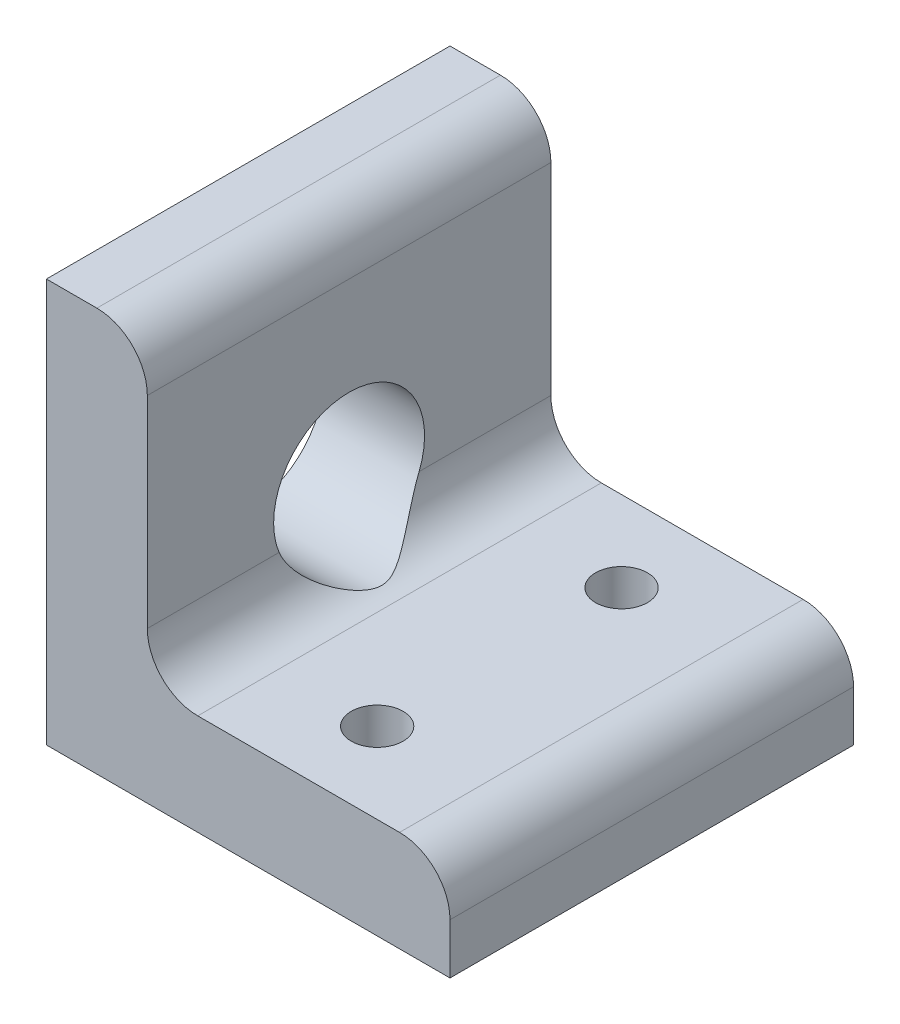
SolidWorks part; units mm, degrees
ref_plane "Front Plane" through (0, 0, 0) normal (0, 0, 1) x (1, 0, 0)
ref_plane "Top Plane" through (0, 0, 0) normal (0, 1, 0) x (1, 0, 0)
ref_plane "Right Plane" through (0, 0, 0) normal (1, 0, 0) x (0, 0, -1)
sketch "Sketch1" plane through (0, 0, 0) normal (0, 0, 1) x (1, 0, 0)
  line L1 (0, 0) -> (25.4, 0)
  line L2 (0, 0) -> (0, 25.4)
  line L3 (0, 25.4) -> (25.4, 25.4)
  line L4 (25.4, 0) -> (25.4, 25.4)
  line L5 (25.4, 25.4) -> (6.35, 25.4)
  line L6 (25.4, 25.4) -> (25.4, 6.35)
  line L7 (25.4, 6.35) -> (6.35, 6.35)
  line L8 (6.35, 25.4) -> (6.35, 6.35)
  dimension "D1" = 25.4
  dimension "D2" = 25.4
  dimension "D3" = 19.05
  dimension "D4" = 19.05
extrude "Boss-Extrude1" add sketch "Sketch1" along normal blind 25.4 contours L8 L3 L2 L1 L4 L7
hole_wizard "#4 Clearance Hole1" positions "Sketch5" profile "Sketch4" hole size "#4" standard "ANSI Inch" end condition through all
sketch "Sketch5" plane through (0, 6.35, 0) normal (0, 1, 0) x (1, 0, 0)
  point P0 (15.7352, -20.32)
  point P2 (15.875, -5.08)
  dimension "D1" = 15.875
  dimension "D2" = 15.7352
  dimension "D3" = 5.08
  dimension "D4" = 20.32
sketch "Sketch4" plane through (15.7352, 6.35, 20.32) normal (1, 0, 0) x (0, 0, 1)
  line L0 (0, 0) -> (0, 6.35)
  line L1 (0, 6.35) -> (1.6319, 6.35)
  line L2 (1.6319, 6.35) -> (1.6319, 0)
  line L5 (1.6319, 0) -> (0, 0)
  line L11 (0, -6.35) -> (0, 107.95) construction
  dimension "Thru Hole Dia." = 3.2639
  dimension "Thru Hole Depth" = 6.35
fillet "Fillet1" radius 3.175 3 edges at (25.4, 6.35, 12.7) (6.35, 6.35, 12.7) (6.35, 25.4, 12.7)
hole_wizard "3/8 (0.374) Diameter Hole1" positions "Sketch6" profile "Sketch7" hole size "3/8" standard "ANSI Inch" end condition through all
sketch "Sketch6" plane through (0, 0, 0) normal (1, 0, 0) x (0, 0, -1)
  line L0 (0, 22.225) -> (0, 9.525) construction
  point P2 (-12.7, 11.303)
  dimension "D2" = 11.303
  dimension "D3" = 12.7
sketch "Sketch7" plane through (0, 11.303, 12.7) normal (0, 1, 0) x (0, 0, 1)
  line L0 (0, 0) -> (0, 25.4)
  line L1 (0, 25.4) -> (4.7498, 25.4)
  line L2 (4.7498, 25.4) -> (4.7498, 0)
  line L5 (4.7498, 0) -> (0, 0)
  line L11 (0, -6.35) -> (0, 107.95) construction
  dimension "Thru Hole Dia." = 9.4996
  dimension "Thru Hole Depth" = 25.4
